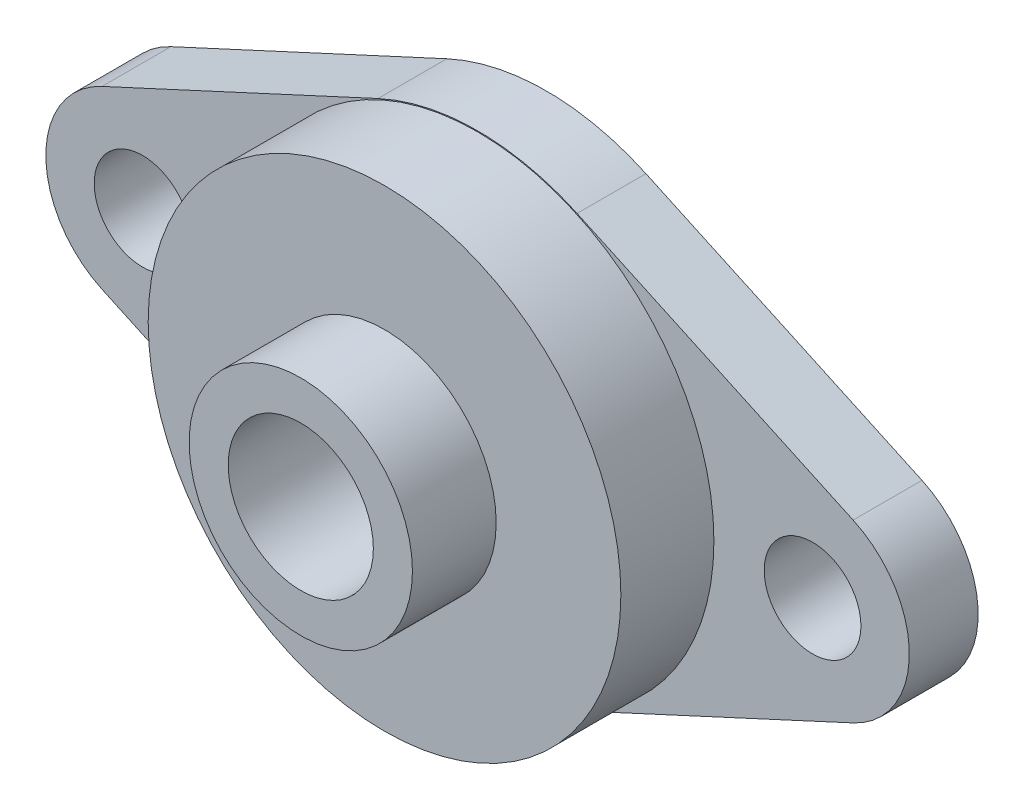
SolidWorks part; units mm, degrees
ref_plane "前基準面" through (0, 0, 0) normal (0, 0, 1) x (1, 0, 0)
ref_plane "上基準面" through (0, 0, 0) normal (0, 1, 0) x (1, 0, 0)
ref_plane "右基準面" through (0, 0, 0) normal (1, 0, 0) x (0, 0, -1)
sketch "草圖2" plane through (0, 0, 0) normal (0, 0, 1) x (1, 0, 0)
  line L0 (-18, 0) -> (18, 0) construction
  line L1 (-20.1811, 4.7205) -> (-5.3479, 11.5742)
  line L2 (0, 12.75) -> (0, -12.75) construction
  line L3 (20.1811, 4.7205) -> (5.3479, 11.5742)
  line L4 (20.1811, -4.7205) -> (5.3479, -11.5742)
  line L5 (-20.1811, -4.7205) -> (-5.3479, -11.5742)
  circle A0 centre (-18, 0) radius 2.6
  circle A1 centre (18, 0) radius 2.6
  arc A2 (-5.3479, -11.5742) -> (5.3479, -11.5742) centre (0, 0) ccw
  arc A3 (-20.1811, 4.7205) -> (-20.1811, -4.7205) centre (-18, 0) ccw
  arc A4 (20.1811, -4.7205) -> (20.1811, 4.7205) centre (18, 0) ccw
  arc A5 (5.3479, 11.5742) -> (-5.3479, 11.5742) centre (0, 0) ccw
  circle A7 centre (0, 0) radius 3.9
  dimension "D2" = 25.5
  dimension "D4" = 10.4
  dimension "D5" = 10.4
  dimension "D1" = 36
  dimension "D3" = 18
extrude "填料-伸長1" add sketch "草圖2" along normal blind 3.7
sketch "草圖3" plane through (0, 0, 3.7) normal (0, 0, 1) x (1, 0, 0)
  circle A0 centre (0, 0) radius 12.7
  circle A1 centre (0, 0) radius 3.9
extrude "填料-伸長2" add sketch "草圖3" along normal blind 5
sketch "草圖4" plane through (0, 0, 8.7) normal (0, 0, 1) x (1, 0, 0)
  circle A0 centre (0, 0) radius 6
  circle A1 centre (0, 0) radius 3.9
extrude "填料-伸長3" add sketch "草圖4" along normal blind 4.5
